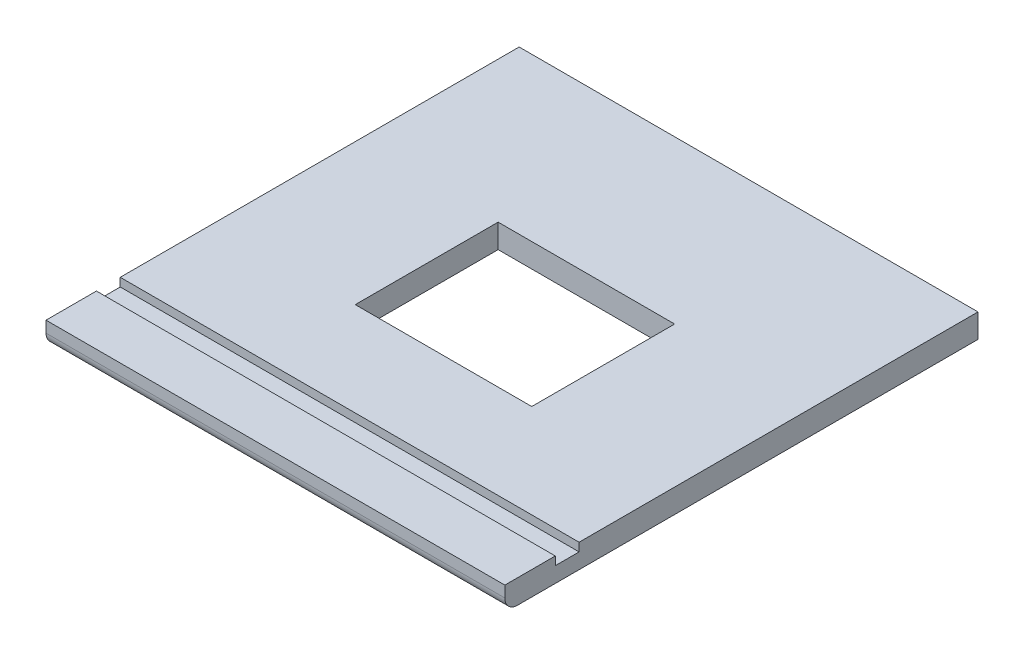
SolidWorks part; units mm, degrees
ref_plane "Front Plane" through (0, 0, 0) normal (0, 0, 1) x (1, 0, 0)
ref_plane "Top Plane" through (0, 0, 0) normal (0, 1, 0) x (1, 0, 0)
ref_plane "Right Plane" through (0, 0, 0) normal (1, 0, 0) x (0, 0, -1)
sketch "Sketch1" plane through (0, 0, 0) normal (0, 1, 0) x (1, 0, 0)
  line L1 (0, 0) -> (346.7, 0)
  line L2 (0, 0) -> (0, -357.5)
  line L3 (0, -357.5) -> (346.7, -357.5)
  line L4 (346.7, 0) -> (346.7, -357.5)
  dimension "D1" = 346.7
  dimension "D2" = 357.5
extrude "Boss-Extrude1" add sketch "Sketch1" along normal blind 18
sketch "Sketch2" plane through (0, 18, 0) normal (0, 1, 0) x (1, 0, 0)
  line L0 (0, -357.5) -> (346.7, -357.5) construction
  line L1 (346.7, -319.4) -> (0, -319.4)
  line L2 (346.7, -319.4) -> (346.7, -301.4)
  line L3 (346.7, -301.4) -> (0, -301.4)
  line L4 (0, -319.4) -> (0, -301.4)
  line L5 (0, 0) -> (0, -357.5) construction
  line L6 (346.7, -357.5) -> (346.7, 0) construction
  dimension "D1" = 18
  dimension "D2" = 38.1
  dimension "D3" = 0
  dimension "D4" = 0
extrude "Cut-Extrude1" cut sketch "Sketch2" against normal blind 6.35
sketch "Sketch3" plane through (0, 18, 0) normal (0, 1, 0) x (1, 0, 0)
  line L0 (0, -357.5) -> (346.7, -357.5) construction
  line L1 (106.675, -230.5) -> (240.025, -230.5)
  line L2 (106.675, -230.5) -> (106.675, -122.55)
  line L3 (106.675, -122.55) -> (240.025, -122.55)
  line L4 (240.025, -230.5) -> (240.025, -122.55)
  point P7 (173.35, -230.5)
  point P8 (173.35, -357.5)
  point P9 (106.675, -176.525)
  dimension "D1" = 107.95
  dimension "D2" = 133.35
  dimension "D3" = 0
  dimension "D4" = 180.975
extrude "Cut-Extrude3" cut sketch "Sketch3" against normal through all
fillet "Fillet1" radius 9.525 1 edges at (173.35, 0, 357.5)
